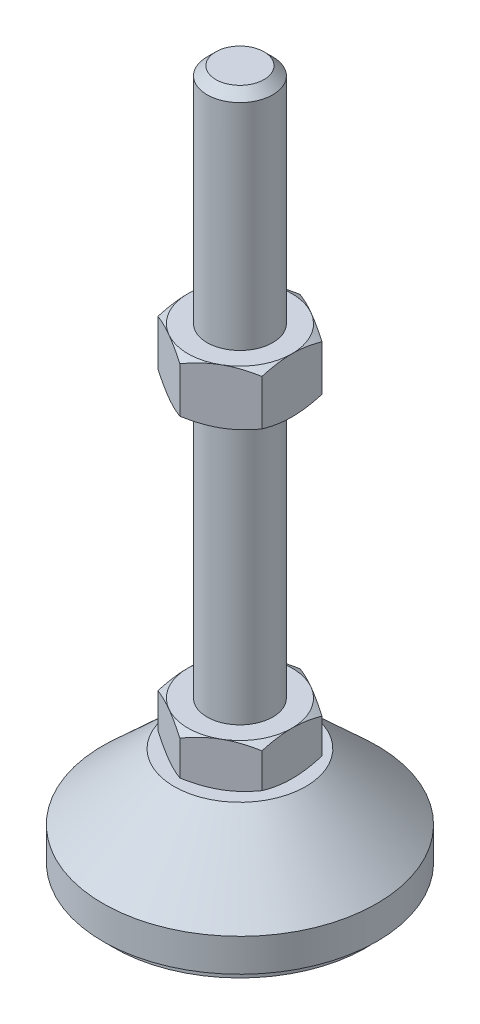
SolidWorks part; units mm, degrees
ref_plane "Спереди" through (0, 0, 0) normal (0, 0, 1) x (1, 0, 0)
ref_plane "Сверху" through (0, 0, 0) normal (0, 1, 0) x (1, 0, 0)
ref_plane "Справа" through (0, 0, 0) normal (1, 0, 0) x (0, 0, -1)
sketch "Эскиз1" plane through (0, 0, 0) normal (0, 0, 1) x (1, 0, 0)
  line L0 (0, 0) -> (-23, 0)
  line L1 (-23, 0) -> (-23, 2)
  line L2 (-23, 2) -> (-25, 2)
  line L3 (-25, 2) -> (-25, 8)
  line L4 (-25, 8) -> (-12, 20)
  line L5 (-12, 20) -> (-6, 20)
  line L12 (-6, 28) -> (-6, 126.4)
  line L13 (-6, 126.4) -> (-4.4, 128)
  line L14 (-4.4, 128) -> (0, 128)
  line L15 (0, 128) -> (0, 0) construction
  line L16 (-6, 20) -> (0, 20) construction
  line L17 (0, 0) -> (0, 128)
  line L18 (0, 0) -> (0, -7.9595) construction
  line L19 (-6, 28) -> (-6, 20)
  point P8 (-6, 77.2)
  point P23 (-9, 20)
  dimension "D1" = 12
  dimension "D2" = 20
  dimension "D3" = 8
  dimension "D4" = 50
  dimension "D5" = 6
  dimension "D6" = 1.6
  dimension "D7" = 45
  dimension "D8" = 24
  dimension "D9" = 2
  dimension "D10" = 100
  dimension "D11" = 6
revolve "Повернуть1" add sketch "Эскиз1" angle 360 about L17
sketch "Эскиз2" plane through (0, 20, 0) normal (0, 1, 0) x (1, 0, 0)
  line L1 (0, 10.9697) -> (-9.5, 5.4848)
  line L2 (-9.5, 5.4848) -> (-9.5, -5.4848)
  line L3 (-9.5, -5.4848) -> (0, -10.9697)
  line L4 (0, -10.9697) -> (9.5, -5.4848)
  line L5 (9.5, -5.4848) -> (9.5, 5.4848)
  line L6 (9.5, 5.4848) -> (0, 10.9697)
  circle A0 centre (0, 0) radius 9.5 construction
  dimension "D1" = 19
extrude "Бобышка-Вытянуть1" add sketch "Эскиз2" along normal up to vertex (8 mm away) up to point (-6, 28, 0)
ref_plane "Плоскость1" through (0, 77.2, 0) normal (0, 1, 0) x (1, 0, 0)
sketch "Эскиз3" plane through (0, 77.2, 0) normal (0, 1, 0) x (1, 0, 0)
  line L6 (9.5, 5.4848) -> (0, 10.9697)
  line L7 (0, 10.9697) -> (-9.5, 5.4848)
  line L8 (-9.5, 5.4848) -> (-9.5, -5.4848)
  line L9 (-9.5, -5.4848) -> (0, -10.9697)
  line L10 (0, -10.9697) -> (9.5, -5.4848)
  line L11 (9.5, -5.4848) -> (9.5, 5.4848)
  line L12 (9.5, 5.4848) -> (0, 10.9697)
  line L13 (0, 10.9697) -> (-9.5, 5.4848)
  line L14 (-9.5, 5.4848) -> (-9.5, -5.4848)
  line L15 (-9.5, -5.4848) -> (0, -10.9697)
  line L16 (0, -10.9697) -> (9.5, -5.4848)
  line L17 (9.5, -5.4848) -> (9.5, 5.4848)
  dimension "D1" = 0
extrude "Бобышка-Вытянуть2" add sketch "Эскиз3" along normal blind 10
sketch "Эскиз4" plane through (0, 0, 0) normal (0, 0, 1) x (1, 0, 0)
  line L0 (-9.5, 87.2) -> (-18.1603, 82.2)
  line L1 (-18.1603, 82.2) -> (-18.1603, 87.2)
  line L2 (-18.1603, 87.2) -> (-9.5, 87.2)
  line L3 (-18.1603, 82.2) -> (-9.5, 77.2)
  line L4 (50, 77.2) -> (-50, 77.2) construction
  line L5 (-9.5, 77.2) -> (-18.1603, 77.2)
  line L6 (-18.1603, 77.2) -> (-18.1603, 82.2)
  line L7 (-9.5, 87.2) -> (-9.5, 77.2) construction
  line L8 (-9.5, 28) -> (-16.4282, 28)
  line L9 (-16.4282, 28) -> (-16.4282, 24)
  line L10 (-16.4282, 24) -> (-9.5, 28)
  line L11 (-9.5, 20) -> (-16.4282, 24)
  line L12 (-16.4282, 24) -> (-16.4282, 20)
  line L13 (-16.4282, 20) -> (-9.5, 20)
  line L14 (0, 128) -> (0, 96.3793) construction
  dimension "D1" = 30
  dimension "D2" = 30
revolve "Вырез-Повернуть2" cut sketch "Эскиз4" angle 360 about L14
